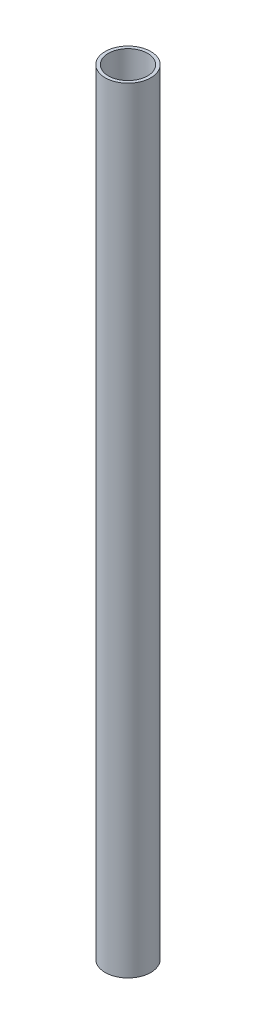
SolidWorks part; units mm, degrees
ref_plane "Front Plane" through (0, 0, 0) normal (0, 0, 1) x (1, 0, 0)
ref_plane "Top Plane" through (0, 0, 0) normal (0, 1, 0) x (1, 0, 0)
ref_plane "Right Plane" through (0, 0, 0) normal (1, 0, 0) x (0, 0, -1)
sketch "Sketch1" plane through (0, 0, 0) normal (0, 1, 0) x (1, 0, 0)
  circle A0 centre (0, 0) radius 12.7
extrude "Boss-Extrude1" add sketch "Sketch1" along normal blind 431.8
sketch "Sketch2" plane through (0, 0, 0) normal (0, -1, 0) x (1, 0, 0)
  circle A0 centre (0, 0) radius 10.922
extrude "Cut-Extrude1" cut sketch "Sketch2" against normal through all
